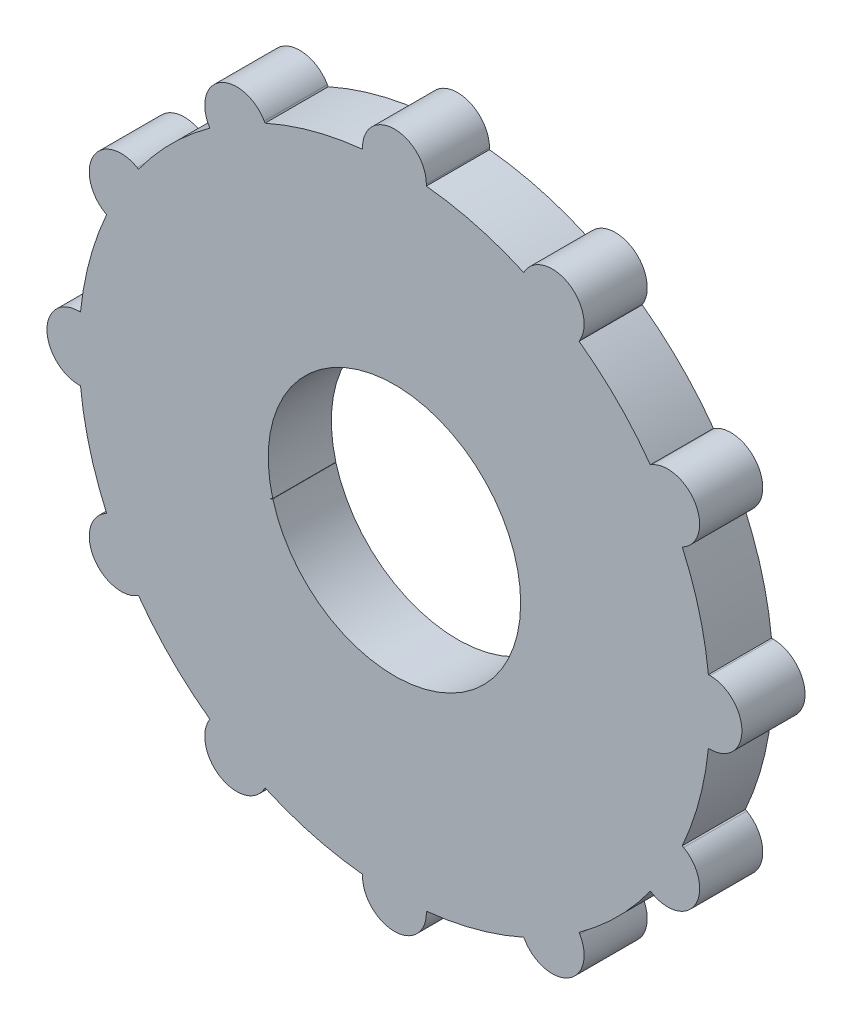
SolidWorks part; units mm, degrees
ref_plane "Front Plane" through (0, 0, 0) normal (0, 0, 1) x (1, 0, 0)
ref_plane "Top Plane" through (0, 0, 0) normal (0, 1, 0) x (1, 0, 0)
ref_plane "Right Plane" through (0, 0, 0) normal (1, 0, 0) x (0, 0, -1)
sketch "Sketch1" plane through (0, 0, 0) normal (0, 0, 1) x (1, 0, 0)
  line L0 (0, 20) -> (0, 50) construction
  line L1 (-5.0555, 49.7438) -> (-5.0555, 50)
  line L3 (10, 17.3205) -> (25, 43.3013) construction
  line L4 (20.4936, 45.6071) -> (20.6218, 45.829)
  line L5 (29.2501, 40.5516) -> (29.3782, 40.7735)
  line L6 (17.3205, 10) -> (43.3013, 25) construction
  line L7 (40.5516, 29.2501) -> (40.7735, 29.3782)
  line L8 (45.6071, 20.4936) -> (45.829, 20.6218)
  line L9 (20, 0) -> (50, 0) construction
  line L10 (49.7438, 5.0555) -> (50, 5.0555)
  line L11 (49.7438, -5.0555) -> (50, -5.0555)
  line L12 (17.3205, -10) -> (43.3013, -25) construction
  line L13 (45.6071, -20.4936) -> (45.829, -20.6218)
  line L14 (40.5516, -29.2501) -> (40.7735, -29.3782)
  line L15 (10, -17.3205) -> (25, -43.3013) construction
  line L18 (0, -20) -> (0, -50) construction
  line L20 (-5.0555, -49.7438) -> (-5.0555, -50)
  line L21 (-10, -17.3205) -> (-25, -43.3013) construction
  line L22 (-20.4936, -45.6071) -> (-20.6218, -45.829)
  line L23 (-29.2501, -40.5516) -> (-29.3782, -40.7735)
  line L24 (-17.3205, -10) -> (-43.3013, -25) construction
  line L26 (-19.8483, -5.6218) -> (-18.8676, -5.0555)
  line L27 (-20, 0) -> (-50, 0) construction
  line L28 (-49.7438, -5.0555) -> (-50, -5.0555)
  line L30 (-17.3205, 10) -> (-43.3013, 25) construction
  line L33 (-10, 17.3205) -> (-25, 43.3013) construction
  line L34 (-29.2501, 40.5516) -> (-29.3782, 40.7735)
  line L35 (-20.4936, 45.6071) -> (-20.6218, 45.829)
  line L48 (-45.6071, -20.4936) -> (-45.829, -20.6218)
  line L49 (-40.5516, -29.2501) -> (-40.7735, -29.3782)
  line L50 (-45.6071, 20.4936) -> (-45.829, 20.6218)
  line L51 (-40.5516, 29.2501) -> (-40.7735, 29.3782)
  line L55 (5.0555, -49.7438) -> (5.0555, -50)
  line L56 (20.4936, -45.6071) -> (20.6218, -45.829)
  line L57 (29.2501, -40.5516) -> (29.3782, -40.7735)
  line L58 (-49.7438, 5.0555) -> (-50, 5.0555)
  line L59 (5.0555, 49.7438) -> (5.0555, 50)
  circle A0 centre (0, 0) radius 20
  arc A2 (-45.6071, 20.4936) -> (-49.7438, 5.0555) centre (0, 0) ccw
  arc A4 (-5.0555, 20) -> (-5.015, 19.361) centre (0, 20) ccw
  arc A5 (5.0555, 50) -> (-5.0555, 50) centre (0, 50) ccw
  arc A6 (5.6218, 19.8483) -> (5.3374, 19.2747) centre (10, 17.3205) ccw
  arc A7 (29.3782, 40.7735) -> (20.6218, 45.829) centre (25, 43.3013) ccw
  arc A8 (14.7927, 14.3782) -> (14.2596, 14.0236) centre (17.3205, 10) ccw
  arc A9 (45.829, 20.6218) -> (40.7735, 29.3782) centre (43.3013, 25) ccw
  arc A10 (20, 5.0555) -> (19.361, 5.015) centre (20, 0) ccw
  arc A11 (50, -5.0555) -> (50, 5.0555) centre (50, 0) ccw
  arc A12 (19.8483, -5.6218) -> (19.2747, -5.3374) centre (17.3205, -10) ccw
  arc A13 (40.7735, -29.3782) -> (45.829, -20.6218) centre (43.3013, -25) ccw
  arc A14 (14.3782, -14.7927) -> (14.0236, -14.2596) centre (10, -17.3205) ccw
  arc A15 (20.6218, -45.829) -> (29.3782, -40.7735) centre (25, -43.3013) ccw
  arc A16 (5.0555, -20) -> (5.015, -19.361) centre (0, -20) ccw
  arc A17 (-5.0555, -50) -> (5.0555, -50) centre (0, -50) ccw
  arc A18 (-5.6218, -19.8483) -> (-5.3374, -19.2747) centre (-10, -17.3205) ccw
  arc A19 (-29.3782, -40.7735) -> (-20.6218, -45.829) centre (-25, -43.3013) ccw
  arc A20 (-14.7927, -14.3782) -> (-14.2596, -14.0236) centre (-17.3205, -10) ccw
  arc A21 (-45.829, -20.6218) -> (-40.7735, -29.3782) centre (-43.3013, -25) ccw
  arc A22 (-20, -5.0555) -> (-19.361, -5.015) centre (-20, 0) ccw
  arc A23 (-50, 5.0555) -> (-50, -5.0555) centre (-50, 0) ccw
  arc A24 (-19.8483, 5.6218) -> (-19.2747, 5.3374) centre (-17.3205, 10) ccw
  arc A25 (-40.7735, 29.3782) -> (-45.829, 20.6218) centre (-43.3013, 25) ccw
  arc A26 (-14.3782, 14.7927) -> (-14.0236, 14.2596) centre (-10, 17.3205) ccw
  arc A27 (-20.6218, 45.829) -> (-29.3782, 40.7735) centre (-25, 43.3013) ccw
  arc A28 (-14.2596, 14.0236) -> (-14.7927, 14.3782) centre (-17.3205, 10) ccw
  arc A31 (-19.361, 5.015) -> (-20, 5.0555) centre (-20, 0) ccw
  arc A34 (-19.2747, -5.3374) -> (-19.8483, -5.6218) centre (-17.3205, -10) ccw
  arc A37 (-14.0236, -14.2596) -> (-14.3782, -14.7927) centre (-10, -17.3205) ccw
  arc A40 (40.5516, 29.2501) -> (29.2501, 40.5516) centre (0, 0) ccw
  arc A41 (-5.3374, 19.2747) -> (-5.6218, 19.8483) centre (-10, 17.3205) ccw
  arc A44 (5.015, 19.361) -> (5.0555, 20) centre (0, 20) ccw
  arc A45 (14.0236, 14.2596) -> (14.3782, 14.7927) centre (10, 17.3205) ccw
  arc A46 (19.2747, 5.3374) -> (19.8483, 5.6218) centre (17.3205, 10) ccw
  arc A47 (19.361, -5.015) -> (20, -5.0555) centre (20, 0) ccw
  arc A48 (14.2596, -14.0236) -> (14.7927, -14.3782) centre (17.3205, -10) ccw
  arc A49 (5.3374, -19.2747) -> (5.6218, -19.8483) centre (10, -17.3205) ccw
  arc A50 (-5.015, -19.361) -> (-5.0555, -20) centre (0, -20) ccw
  arc A51 (29.2501, -40.5516) -> (40.5516, -29.2501) centre (0, 0) ccw
  arc A52 (5.0555, -49.7438) -> (20.4936, -45.6071) centre (0, 0) ccw
  arc A53 (-20.4936, -45.6071) -> (-5.0555, -49.7438) centre (0, 0) ccw
  arc A54 (-49.7438, -5.0555) -> (-45.6071, -20.4936) centre (0, 0) ccw
  arc A55 (-5.0555, 49.7438) -> (-20.4936, 45.6071) centre (0, 0) ccw
  arc A56 (-40.5516, -29.2501) -> (-29.2501, -40.5516) centre (0, 0) ccw
  arc A57 (20.4936, 45.6071) -> (5.0555, 49.7438) centre (0, 0) ccw
  arc A58 (49.7438, 5.0555) -> (45.6071, 20.4936) centre (0, 0) ccw
  arc A59 (45.6071, -20.4936) -> (49.7438, -5.0555) centre (0, 0) ccw
  arc A60 (-29.2501, 40.5516) -> (-40.5516, 29.2501) centre (0, 0) ccw
  point P8 (0, 35)
  point P14 (0, 0)
  point P17 (17.5, 30.3109)
  point P24 (30.3109, 17.5)
  point P31 (35, 0)
  point P38 (30.3109, -17.5)
  point P45 (17.5, -30.3109)
  point P52 (0, -35)
  point P59 (-17.5, -30.3109)
  point P66 (-30.3109, -17.5)
  point P73 (-35, 0)
  point P80 (-30.3109, 17.5)
  point P87 (-17.5, 30.3109)
  point P92 (0, 0)
  point P93 (-30.3109, 17.5)
  point P104 (-35, 0)
  point P113 (-30.3109, -17.5)
  point P122 (-17.5, -30.3109)
  point P138 (-17.5, 30.3109)
extrude "Boss-Extrude1" add sketch "Sketch1" along normal blind 10 contours L34 A60 L51 A25 L50 A2 L58 A23 L28 A54 L48 A21 L49 A56 L23 A19 L22 A53 L20 A17 L55 A52 L56 A15 L57 A51 L14 A13 L13 A59 L11 A11 L10 A58 L8 A9 L7 A40 L5 A7 L4 A57 L59 A5 L1 A55 L35 A27 A0 A34
